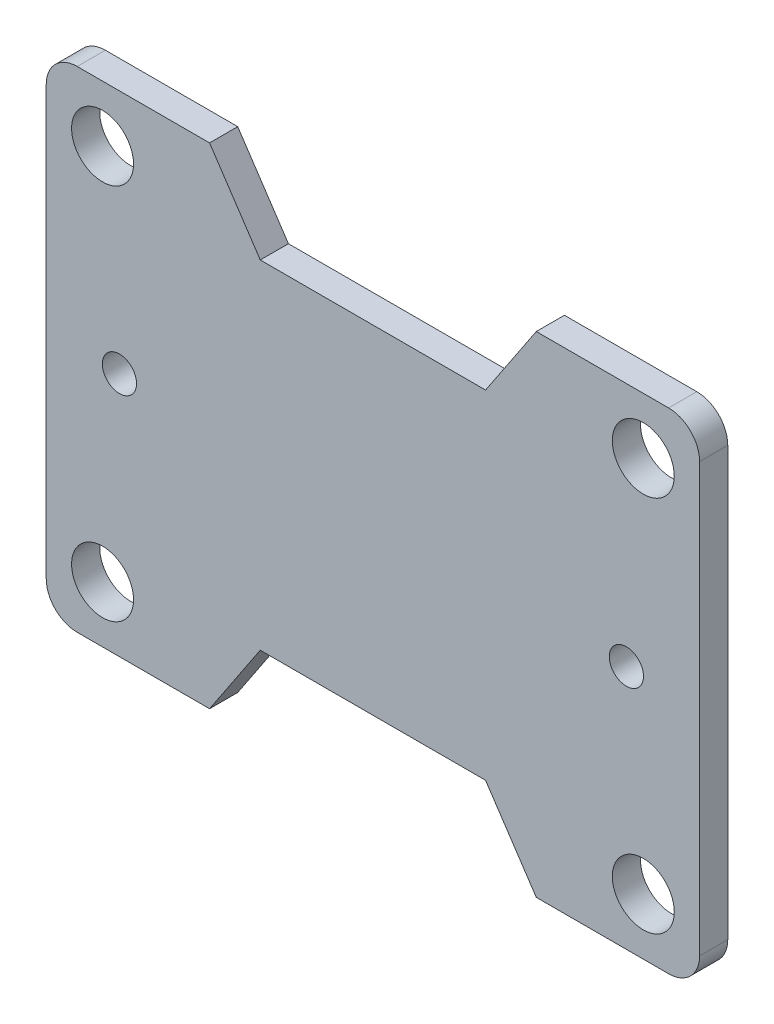
SolidWorks part; units mm, degrees
ref_plane "前视基准面" through (0, 0, 0) normal (0, 0, 1) x (1, 0, 0)
ref_plane "上视基准面" through (0, 0, 0) normal (0, 1, 0) x (1, 0, 0)
ref_plane "右视基准面" through (0, 0, 0) normal (1, 0, 0) x (0, 0, -1)
sketch "Sketch1" plane through (0, 0, 0) normal (0, 0, 1) x (1, 0, 0)
  line L0 (0, 33.5) -> (0, 36.25)
  line L1 (0, 0) -> (48, 0)
  line L2 (0, 0) -> (0, 33.5)
  line L3 (0, 33.5) -> (48, 33.5)
  line L4 (48, 0) -> (48, 33.5)
  line L5 (48, 33.5) -> (48, 36.25)
  line L6 (0, 0) -> (0, -2.75)
  line L7 (0, 2.75) -> (0, 30.75)
  line L8 (48, 0) -> (48, -2.75)
  line L9 (0, 16.75) -> (48, 16.75)
  line L10 (46.5, 16.75) -> (46.5, 18.27)
  line L11 (46.5, 16.75) -> (1.5, 16.75)
  line L12 (1.5, 16.75) -> (1.5, 18.27)
  line L13 (24, 16.75) -> (1.5, 16.75)
  line L14 (24, 16.75) -> (46.5, 16.75)
  line L15 (24, 33.5) -> (24, 38.5)
  line L16 (0, 16.75) -> (-5, 16.75)
  line L17 (-5, 16.75) -> (-5, 38.5)
  line L18 (-5, 38.5) -> (24, 38.5)
  line L19 (48, 16.75) -> (53, 16.75)
  line L20 (24, 0) -> (24, -5)
  line L21 (24, -5) -> (-5, -5)
  line L22 (-5, -5) -> (-5, 16.75)
  line L23 (24, -5) -> (53, -5)
  line L24 (53, -5) -> (53, 16.75)
  line L25 (53, 16.75) -> (53, 38.5)
  line L26 (53, 38.5) -> (24, 38.5)
  line L27 (24, 16.75) -> (24, 31.75)
  line L28 (24, 16.75) -> (24, 1.75)
  line L29 (24, 1.75) -> (14, 1.75)
  line L30 (14, 1.75) -> (24, 1.75)
  line L31 (24, 1.75) -> (34, 1.75)
  line L32 (24, 31.75) -> (14, 31.75)
  line L33 (14, 31.75) -> (34, 31.75)
  line L34 (34, 31.75) -> (38.5, 38.5)
  line L35 (38.5, 38.5) -> (9.5, 38.5)
  line L36 (9.5, 38.5) -> (14, 31.75)
  line L37 (9.5, -5) -> (14, 1.75)
  line L38 (34, 1.75) -> (38.5, -5)
  line L39 (38.5, -5) -> (9.5, -5)
  circle A0 centre (0, 33.5) radius 2.75
  circle A1 centre (48, 33.5) radius 2.75
  circle A2 centre (0, 0) radius 2.75
  circle A3 centre (48, 0) radius 2.75
  circle A4 centre (46.5, 16.75) radius 1.52
  circle A5 centre (1.5, 16.75) radius 1.52
  dimension "D1" = 2.75
  dimension "D2" = 48
  dimension "D3" = 2.75
  dimension "D4" = 2.75
  dimension "D5" = 28
  dimension "D6" = 2.75
  dimension "D7" = 1.52
  dimension "D8" = 1.52
  dimension "D9" = 22.5
  dimension "D10" = 22.5
  dimension "D11" = 5
  dimension "D12" = 5
  dimension "D13" = 5
  dimension "D14" = 5
  dimension "D15" = 15
  dimension "D16" = 15
  dimension "D17" = 10
  dimension "D18" = 10
extrude "Boss-Extrude1" add sketch "Sketch1" along normal blind 2.5 contours A5 L16 L22 L21 L37 L1 A2 L2 | A5 L2 A0 L3 L36 L18 L17 L16 | A5 L13 L27 L32 L36 L3 A0 L2 | A4 L4 A1 L3 L34 L33 L27 L11 | A4 L19 L25 L26 L34 L3 A1 L4 | A4 L4 A3 L1 L38 L23 L24 L19 | A4 L11 L28 L31 L38 L1 A3 L4 | A5 L2 A2 L1 L37 L29 L28 L13
fillet "Fillet1" radius 2.75 4 edges at (53, 38.5, 1.25) (53, -5, 1.25) (-5, -5, 1.25) (-5, 38.5, 1.25)
